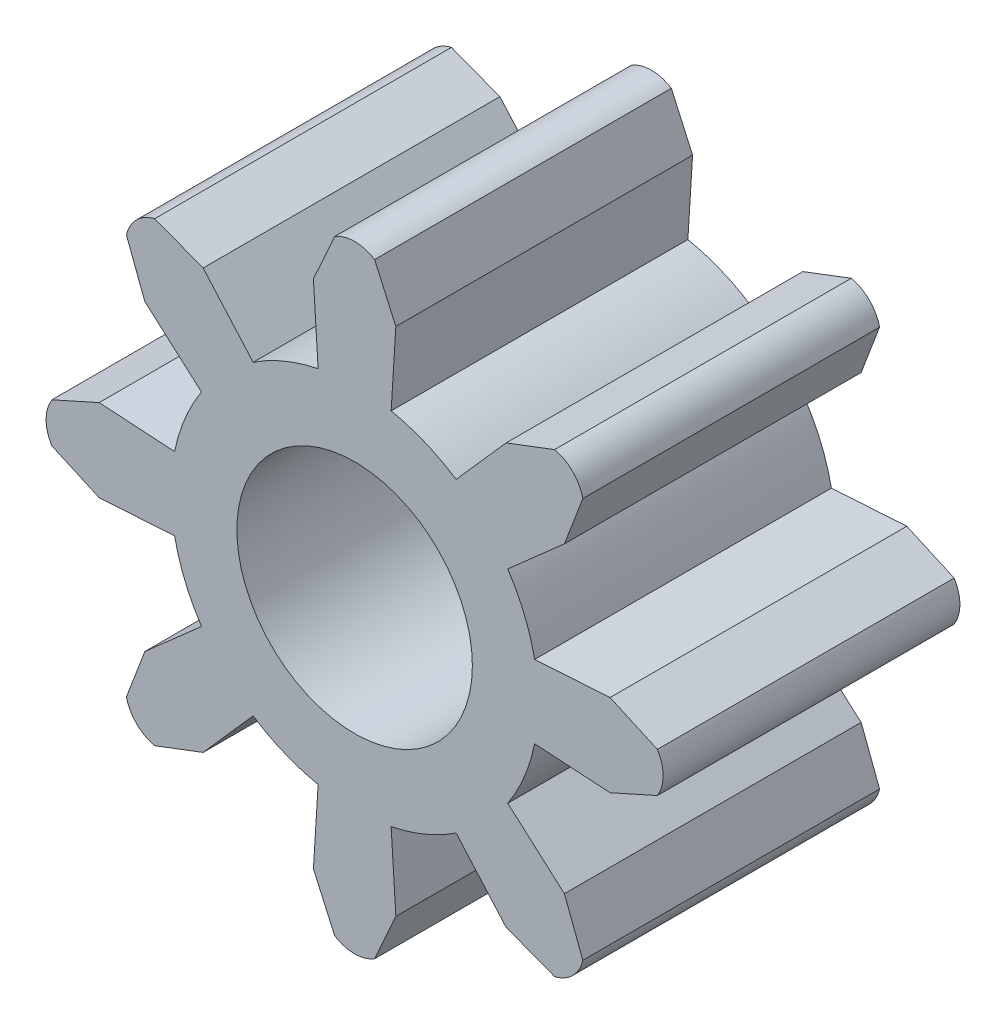
SolidWorks part; units mm, degrees
ref_plane "Przednia" through (0, 0, 0) normal (0, 0, 1) x (1, 0, 0)
ref_plane "Górna" through (0, 0, 0) normal (0, 1, 0) x (1, 0, 0)
ref_plane "Prawa" through (0, 0, 0) normal (1, 0, 0) x (0, 0, -1)
sketch "Szkic1" plane through (0, 0, 0) normal (0, 0, 1) x (1, 0, 0)
  line L0 (0, 0) -> (0, 7.2138) construction
  line L1 (0.875, 5.4234) -> (0.775, 3.8222)
  line L2 (0.875, 5.4234) -> (0.4241, 6.4277)
  line L3 (-0.875, 5.4234) -> (-0.4241, 6.4277)
  line L4 (-0.875, 5.4234) -> (-0.775, 3.8222)
  line L5 (4.4536, 3.2162) -> (3.2507, 2.1547)
  line L6 (4.4536, 3.2162) -> (4.845, 4.2452)
  line L7 (3.2162, 4.4536) -> (4.2452, 4.845)
  line L8 (3.2162, 4.4536) -> (2.1547, 3.2507)
  line L9 (0, 0) -> (5.1009, 5.1009) construction
  line L10 (5.4234, -0.875) -> (3.8222, -0.775)
  line L11 (5.4234, -0.875) -> (6.4277, -0.4241)
  line L12 (5.4234, 0.875) -> (6.4277, 0.4241)
  line L13 (5.4234, 0.875) -> (3.8222, 0.775)
  line L14 (0, 0) -> (7.2138, 0) construction
  line L15 (3.2162, -4.4536) -> (2.1547, -3.2507)
  line L16 (3.2162, -4.4536) -> (4.2452, -4.845)
  line L17 (4.4536, -3.2162) -> (4.845, -4.2452)
  line L18 (4.4536, -3.2162) -> (3.2507, -2.1547)
  line L19 (0, 0) -> (5.1009, -5.1009) construction
  line L20 (-0.875, -5.4234) -> (-0.775, -3.8222)
  line L21 (-0.875, -5.4234) -> (-0.4241, -6.4277)
  line L22 (0.875, -5.4234) -> (0.4241, -6.4277)
  line L23 (0.875, -5.4234) -> (0.775, -3.8222)
  line L24 (0, 0) -> (0, -7.2138) construction
  line L25 (-4.4536, -3.2162) -> (-3.2507, -2.1547)
  line L26 (-4.4536, -3.2162) -> (-4.845, -4.2452)
  line L27 (-3.2162, -4.4536) -> (-4.2452, -4.845)
  line L28 (-3.2162, -4.4536) -> (-2.1547, -3.2507)
  line L29 (0, 0) -> (-5.1009, -5.1009) construction
  line L30 (-5.4234, 0.875) -> (-3.8222, 0.775)
  line L31 (-5.4234, 0.875) -> (-6.4277, 0.4241)
  line L32 (-5.4234, -0.875) -> (-6.4277, -0.4241)
  line L33 (-5.4234, -0.875) -> (-3.8222, -0.775)
  line L34 (0, 0) -> (-7.2138, 0) construction
  line L35 (-3.2162, 4.4536) -> (-2.1547, 3.2507)
  line L36 (-3.2162, 4.4536) -> (-4.2452, 4.845)
  line L37 (-4.4536, 3.2162) -> (-4.845, 4.2452)
  line L38 (-4.4536, 3.2162) -> (-3.2507, 2.1547)
  line L39 (0, 0) -> (-5.1009, 5.1009) construction
  circle A0 centre (0, 0) radius 2.5
  circle A1 centre (0, 0) radius 6.55 construction
  arc A2 (-0.775, 3.8222) -> (0.775, 3.8222) centre (0, 0) ccw construction
  arc A3 (0.4241, 6.4277) -> (0, 6.55) centre (0, 5.7533) ccw
  arc A4 (-0.4241, 6.4277) -> (0, 6.55) centre (0, 5.7533) cw
  circle A5 centre (0, 0) radius 2.5
  arc A6 (4.845, 4.2452) -> (4.6315, 4.6315) centre (4.0682, 4.0682) ccw
  arc A7 (4.2452, 4.845) -> (4.6315, 4.6315) centre (4.0682, 4.0682) cw
  circle A8 centre (0, 0) radius 6.55 construction
  circle A9 centre (0, 0) radius 3.9 construction
  circle A10 centre (0, 0) radius 2.5
  arc A11 (6.4277, -0.4241) -> (6.55, 0) centre (5.7533, 0) ccw
  arc A12 (6.4277, 0.4241) -> (6.55, 0) centre (5.7533, 0) cw
  circle A13 centre (0, 0) radius 6.55 construction
  circle A14 centre (0, 0) radius 3.9 construction
  circle A15 centre (0, 0) radius 2.5
  arc A16 (4.2452, -4.845) -> (4.6315, -4.6315) centre (4.0682, -4.0682) ccw
  arc A17 (4.845, -4.2452) -> (4.6315, -4.6315) centre (4.0682, -4.0682) cw
  circle A18 centre (0, 0) radius 6.55 construction
  circle A19 centre (0, 0) radius 3.9 construction
  circle A20 centre (0, 0) radius 2.5
  arc A21 (-0.4241, -6.4277) -> (0, -6.55) centre (0, -5.7533) ccw
  arc A22 (0.4241, -6.4277) -> (0, -6.55) centre (0, -5.7533) cw
  circle A23 centre (0, 0) radius 6.55 construction
  circle A24 centre (0, 0) radius 3.9 construction
  circle A25 centre (0, 0) radius 2.5
  arc A26 (-4.845, -4.2452) -> (-4.6315, -4.6315) centre (-4.0682, -4.0682) ccw
  arc A27 (-4.2452, -4.845) -> (-4.6315, -4.6315) centre (-4.0682, -4.0682) cw
  circle A28 centre (0, 0) radius 6.55 construction
  circle A29 centre (0, 0) radius 3.9 construction
  circle A30 centre (0, 0) radius 2.5
  arc A31 (-6.4277, 0.4241) -> (-6.55, 0) centre (-5.7533, 0) ccw
  arc A32 (-6.4277, -0.4241) -> (-6.55, 0) centre (-5.7533, 0) cw
  circle A33 centre (0, 0) radius 6.55 construction
  circle A34 centre (0, 0) radius 3.9 construction
  circle A35 centre (0, 0) radius 2.5
  arc A36 (-4.2452, 4.845) -> (-4.6315, 4.6315) centre (-4.0682, 4.0682) ccw
  arc A37 (-4.845, 4.2452) -> (-4.6315, 4.6315) centre (-4.0682, 4.0682) cw
  circle A38 centre (0, 0) radius 6.55 construction
  circle A39 centre (0, 0) radius 3.9 construction
  arc A40 (-0.775, 3.8222) -> (-2.1547, 3.2507) centre (0, 0) ccw
  arc A41 (-3.2507, 2.1547) -> (-3.8222, 0.775) centre (0, 0) ccw
  arc A42 (-3.8222, -0.775) -> (-3.2507, -2.1547) centre (0, 0) ccw
  arc A43 (-2.1547, -3.2507) -> (-0.775, -3.8222) centre (0, 0) ccw
  arc A44 (0.775, -3.8222) -> (2.1547, -3.2507) centre (0, 0) ccw
  arc A45 (3.2507, -2.1547) -> (3.8222, -0.775) centre (0, 0) ccw
  arc A46 (3.8222, 0.775) -> (3.2507, 2.1547) centre (0, 0) ccw
  arc A47 (2.1547, 3.2507) -> (0.775, 3.8222) centre (0, 0) ccw
  point P108 (0, 0)
  dimension "D1" = 5
  dimension "D2" = 13.1
  dimension "D3" = 7.8
  dimension "D4" = 1.75
  dimension "D5" = 1.55
extrude "Dodanie-wyciągnięcie1" add sketch "Szkic1" along normal blind 6.3 contours L8 A47 L1 L2 A3 A4 L3 L4 A40 L35 L36 A36 A37 L37 L38 A41 L30 L31 A31 A32 L32 L33 A42 L25 L26 A26 A27 L27 L28 A43 L20 L21 A21 A22 L22 L23 A44 L15 L16 A16 A17 L17 L18 A45 L10 L11 A11 A12 L12 L13 A46
